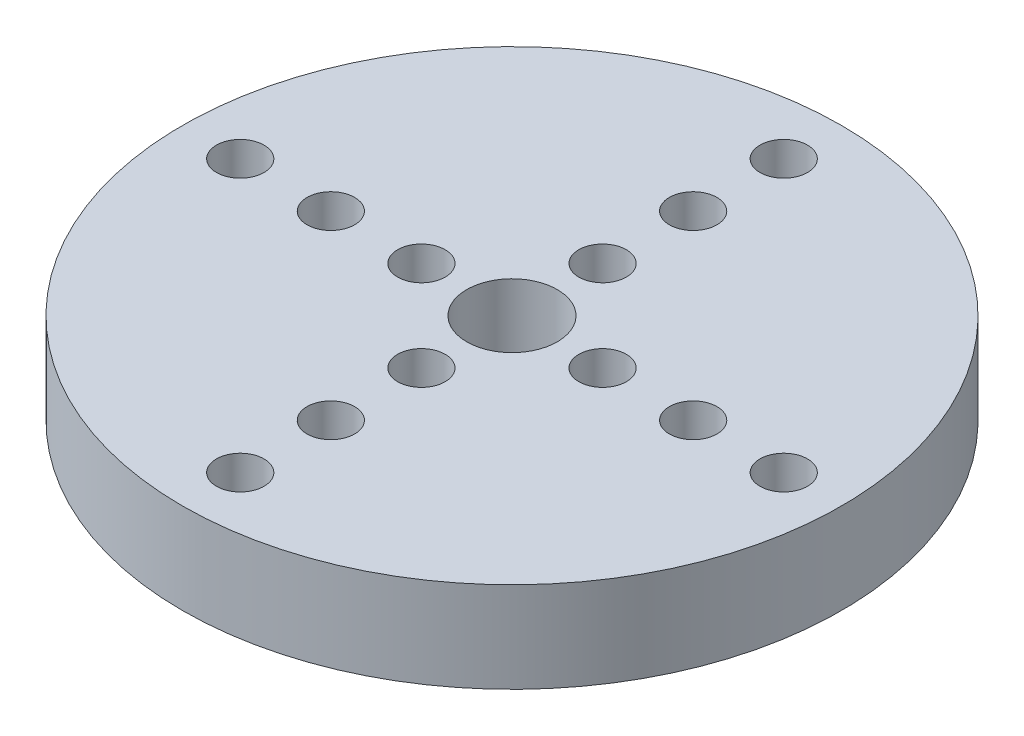
SolidWorks part; units mm, degrees
ref_plane "Front Plane" through (0, 0, 0) normal (0, 0, 1) x (1, 0, 0)
ref_plane "Top Plane" through (0, 0, 0) normal (0, 1, 0) x (1, 0, 0)
ref_plane "Right Plane" through (0, 0, 0) normal (1, 0, 0) x (0, 0, -1)
sketch "스케치1" plane through (0, 0, 0) normal (0, 1, 0) x (1, 0, 0)
  circle A0 centre (0, 0) radius 29.105
extrude "보스-돌출1" add sketch "스케치1" along normal blind 8
sketch "스케치2" plane through (0, 8, 0) normal (0, 1, 0) x (1, 0, 0)
  circle A0 centre (0, 0) radius 4
extrude "컷-돌출1" cut sketch "스케치2" against normal blind 8
sketch "스케치3" plane through (0, 8, 0) normal (0, 1, 0) x (1, 0, 0)
  line L0 (0, 0) -> (0, -50000) construction
  line L1 (0, 0) -> (50000, 0) construction
  circle A0 centre (0, 0) radius 8 construction
  circle A1 centre (0, 0) radius 16 construction
  circle A2 centre (0, 0) radius 24 construction
  circle A3 centre (0, 8) radius 2.1
  circle A4 centre (0, 16) radius 2.1
  circle A5 centre (0, 24) radius 2.1
  circle A6 centre (-8, 0) radius 2.1
  circle A7 centre (-16, 0) radius 2.1
  circle A8 centre (-24, 0) radius 2.1
  circle A9 centre (0, -8) radius 2.1
  circle A10 centre (0, -16) radius 2.1
  circle A11 centre (0, -24) radius 2.1
  circle A12 centre (8, 0) radius 2.1
  circle A13 centre (16, 0) radius 2.1
  circle A14 centre (24, 0) radius 2.1
extrude "컷-돌출2" cut sketch "스케치3" against normal blind 8
